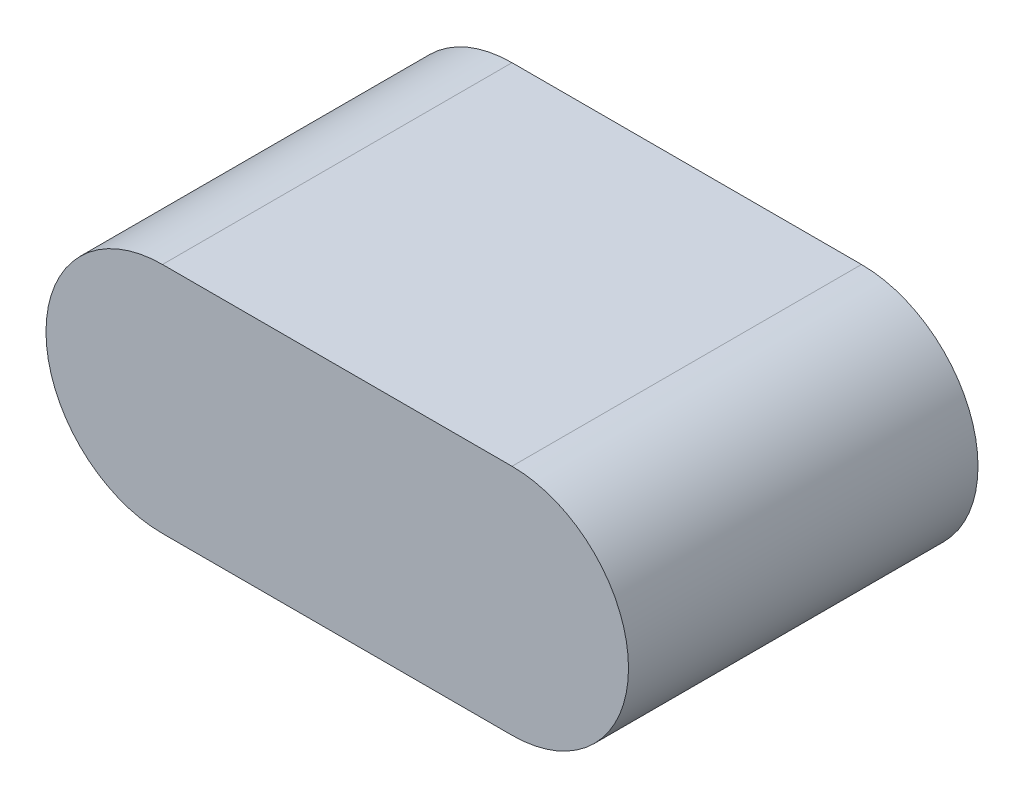
SolidWorks part; units mm, degrees
ref_plane "Front" through (0, 0, 0) normal (0, 0, 1) x (1, 0, 0)
ref_plane "Top" through (0, 0, 0) normal (0, 1, 0) x (1, 0, 0)
ref_plane "Right" through (0, 0, 0) normal (1, 0, 0) x (0, 0, -1)
other "Configuration Table"
sketch "Эскиз1" plane through (0, 0, 0) normal (0, 0, 1) x (1, 0, 0)
  line L0 (-3.519, 0) -> (2.481, 0) construction
  line L1 (-3.519, 2) -> (2.481, 2)
  line L2 (-3.519, -2) -> (2.481, -2)
  arc A0 (-3.519, 2) -> (-3.519, -2) centre (-3.519, 0) ccw
  arc A1 (2.481, -2) -> (2.481, 2) centre (2.481, 0) ccw
  point P3 (-0.519, 0)
  dimension "D2" = 2
  dimension "D1" = 6
extrude "Бобышка-Вытянуть1" add sketch "Эскиз1" along normal blind 6
